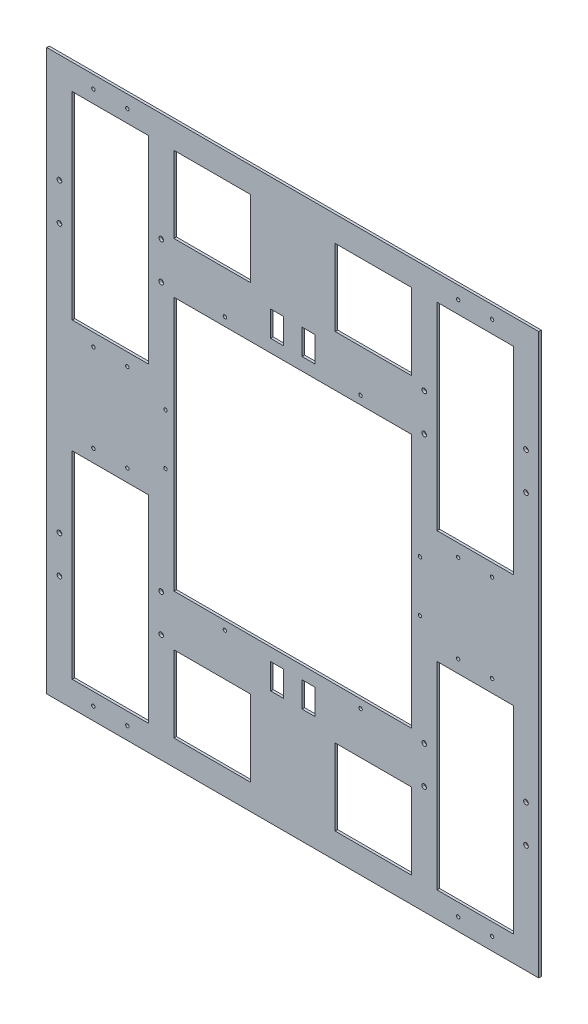
SolidWorks part; units mm, degrees
ref_plane "前基準面" through (0, 0, 0) normal (0, 0, 1) x (1, 0, 0)
ref_plane "上基準面" through (0, 0, 0) normal (0, 1, 0) x (1, 0, 0)
ref_plane "右基準面" through (0, 0, 0) normal (1, 0, 0) x (0, 0, -1)
sketch "草圖1" plane through (0, 0, 0) normal (0, 0, 1) x (1, 0, 0)
  line L1 (-404.7939, 163.224) -> (175.2061, 163.224)
  line L2 (-404.7939, 163.224) -> (-404.7939, -496.776)
  line L3 (-404.7939, -496.776) -> (175.2061, -496.776)
  line L4 (175.2061, 163.224) -> (175.2061, -496.776)
  dimension "D1" = 580
  dimension "D2" = 660
extrude "填料-伸長1" add sketch "草圖1" along normal blind 3
sketch "草圖2" plane through (0, 0, 3) normal (0, 0, 1) x (1, 0, 0)
  line L0 (-404.7939, 163.224) -> (-404.7939, -496.776) construction
  line L1 (-374.7939, -233.546) -> (-284.7939, -233.546)
  line L2 (-374.7939, -233.546) -> (-374.7939, -466.776)
  line L3 (-374.7939, -466.776) -> (-284.7939, -466.776)
  line L4 (-284.7939, -233.546) -> (-284.7939, -466.776)
  line L5 (-404.7939, -496.776) -> (175.2061, -496.776) construction
  line L6 (-114.7939, -496.776) -> (-114.7939, -197.0102)
  line L7 (-404.7939, -166.776) -> (-133.7701, -166.776)
  line L8 (145.2061, -466.776) -> (55.2061, -466.776)
  line L9 (145.2061, -233.546) -> (145.2061, -466.776)
  line L10 (55.2061, -233.546) -> (55.2061, -466.776)
  line L11 (145.2061, -233.546) -> (55.2061, -233.546)
  line L12 (145.2061, -100.006) -> (55.2061, -100.006)
  line L13 (55.2061, -100.006) -> (55.2061, 133.224)
  line L14 (145.2061, -100.006) -> (145.2061, 133.224)
  line L15 (145.2061, 133.224) -> (55.2061, 133.224)
  line L16 (-374.7939, 133.224) -> (-284.7939, 133.224)
  line L17 (-284.7939, -100.006) -> (-284.7939, 133.224)
  line L18 (-374.7939, -100.006) -> (-374.7939, 133.224)
  line L19 (-374.7939, -100.006) -> (-284.7939, -100.006)
  dimension "D1" = 233.23
  dimension "D2" = 90
  dimension "D3" = 30
  dimension "D4" = 30
extrude "除料-伸長1" cut sketch "草圖2" against normal blind 3 contours L13 L15 L14 L12 | L10 L8 L9 L11 | L4 L3 L2 L1 | L17 L16 L18 L19
sketch "草圖3" plane through (0, 0, 3) normal (0, 0, 1) x (1, 0, 0)
  line L0 (-404.7939, 163.224) -> (-404.7939, -496.776) construction
  line L1 (-254.7939, -376.776) -> (-164.7939, -376.776)
  line L2 (-254.7939, -376.776) -> (-254.7939, -466.776)
  line L3 (-254.7939, -466.776) -> (-164.7939, -466.776)
  line L4 (-164.7939, -376.776) -> (-164.7939, -466.776)
  line L5 (-404.7939, -496.776) -> (175.2061, -496.776) construction
  line L6 (-114.7939, -496.776) -> (-114.7939, -197.0102) construction
  line L7 (-114.7939, -197.0102) -> (-114.7939, -297.5966)
  line L8 (-133.7701, -166.776) -> (-254.7939, -166.776)
  line L9 (-404.7939, -166.776) -> (-133.7701, -166.776) construction
  line L10 (25.2061, -376.776) -> (25.2061, -466.776)
  line L11 (25.2061, -466.776) -> (-64.7939, -466.776)
  line L12 (-64.7939, -376.776) -> (-64.7939, -466.776)
  line L13 (25.2061, -376.776) -> (-64.7939, -376.776)
  line L14 (25.2061, 43.224) -> (-64.7939, 43.224)
  line L15 (-64.7939, 43.224) -> (-64.7939, 133.224)
  line L16 (25.2061, 133.224) -> (-64.7939, 133.224)
  line L17 (25.2061, 43.224) -> (25.2061, 133.224)
  line L18 (-164.7939, 43.224) -> (-164.7939, 133.224)
  line L19 (-254.7939, 133.224) -> (-164.7939, 133.224)
  line L20 (-254.7939, 43.224) -> (-254.7939, 133.224)
  line L21 (-254.7939, 43.224) -> (-164.7939, 43.224)
  point P30 (0, 0)
  point P31 (0, 0)
  point P32 (0, 0)
  point P33 (0, 0)
  point P34 (0, 0)
  dimension "D1" = 90
  dimension "D2" = 90
  dimension "D3" = 150
  dimension "D4" = 30
extrude "除料-伸長2" cut sketch "草圖3" against normal through all contours L1 L4 L3 L2 | L12 L11 L10 L13 | L15 L16 L17 L14 | L18 L19 L20 L21
sketch "草圖4" plane through (0, 0, 3) normal (0, 0, 1) x (1, 0, 0)
  line L0 (-404.7939, 163.224) -> (-404.7939, -496.776) construction
  line L1 (-254.7939, -16.776) -> (25.2061, -16.776)
  line L2 (-254.7939, -16.776) -> (-254.7939, -316.776)
  line L3 (-254.7939, -316.776) -> (25.2061, -316.776)
  line L4 (25.2061, -16.776) -> (25.2061, -316.776)
  line L5 (175.2061, 163.224) -> (-404.7939, 163.224) construction
  dimension "D1" = 300
  dimension "D2" = 280
  dimension "D3" = 150
  dimension "D4" = 180
extrude "除料-伸長3" cut sketch "草圖4" against normal blind 3
sketch "草圖5" plane through (0, 0, 3) normal (0, 0, 1) x (1, 0, 0)
  line L1 (-103.7939, -331.776) -> (-88.7939, -331.776)
  line L2 (-103.7939, -331.776) -> (-103.7939, -361.776)
  line L3 (-103.7939, -361.776) -> (-88.7939, -361.776)
  line L4 (-88.7939, -331.776) -> (-88.7939, -361.776)
  line L5 (55.2061, -233.546) -> (55.2061, -466.776) construction
  line L6 (-404.7939, -496.776) -> (175.2061, -496.776) construction
  line L7 (-114.7939, -266.9471) -> (-114.7939, -305.9958)
  line L8 (-114.7939, -496.776) -> (-114.7939, -197.0102) construction
  line L9 (-214.841, -166.776) -> (-181.5469, -166.776)
  line L10 (-404.7939, -166.776) -> (-133.7701, -166.776) construction
  line L11 (-140.7939, -331.776) -> (-140.7939, -361.776)
  line L12 (-125.7939, -361.776) -> (-140.7939, -361.776)
  line L13 (-125.7939, -331.776) -> (-125.7939, -361.776)
  line L14 (-125.7939, -331.776) -> (-140.7939, -331.776)
  line L15 (-125.7939, -1.776) -> (-140.7939, -1.776)
  line L16 (-125.7939, -1.776) -> (-125.7939, 28.224)
  line L17 (-125.7939, 28.224) -> (-140.7939, 28.224)
  line L18 (-140.7939, -1.776) -> (-140.7939, 28.224)
  line L19 (-88.7939, -1.776) -> (-88.7939, 28.224)
  line L20 (-103.7939, 28.224) -> (-88.7939, 28.224)
  line L21 (-103.7939, -1.776) -> (-103.7939, 28.224)
  line L22 (-103.7939, -1.776) -> (-88.7939, -1.776)
  dimension "D1" = 30
  dimension "D2" = 15
  dimension "D3" = 144
  dimension "D4" = 135
extrude "除料-伸長4" cut sketch "草圖5" against normal blind 3 contours L14 L11 L12 L13 | L1 L4 L3 L2 | L17 L18 L15 L16 | L20 L19 L22 L21
sketch "草圖6" plane through (0, 0, 3) normal (0, 0, 1) x (1, 0, 0)
  line L0 (-374.7939, -233.546) -> (-284.7939, -233.546) construction
  line L1 (-284.7939, -233.546) -> (-284.7939, -466.776) construction
  line L2 (-374.7939, -233.546) -> (-374.7939, -466.776) construction
  line L3 (-374.7939, -350.161) -> (-293.3571, -350.161)
  line L4 (-114.7939, -197.0102) -> (-114.7939, -286.0305)
  line L5 (-114.7939, -496.776) -> (-114.7939, -197.0102) construction
  line L6 (-234.4775, -166.776) -> (-164.5146, -166.776)
  line L7 (-404.7939, -166.776) -> (-133.7701, -166.776) construction
  circle A0 centre (-349.7939, -218.546) radius 2
  circle A1 centre (-309.7939, -218.546) radius 2
  circle A2 centre (-309.7939, -481.776) radius 2
  circle A3 centre (-349.7939, -481.776) radius 2
  circle A4 centre (-349.7939, -218.546) radius 2
  circle A5 centre (-309.7939, -218.546) radius 2
  circle A6 centre (-309.7939, -481.776) radius 2
  circle A7 centre (-349.7939, -481.776) radius 2
  circle A8 centre (-349.7939, -218.546) radius 2
  circle A9 centre (-309.7939, -218.546) radius 2
  circle A10 centre (-309.7939, -481.776) radius 2
  circle A11 centre (-349.7939, -481.776) radius 2
  circle A12 centre (-349.7939, -218.546) radius 2
  circle A13 centre (-309.7939, -218.546) radius 2
  circle A14 centre (-309.7939, -481.776) radius 2
  circle A15 centre (-349.7939, -481.776) radius 2
  circle A16 centre (80.2061, -481.776) radius 2
  circle A17 centre (120.2061, -481.776) radius 2
  circle A18 centre (80.2061, -218.546) radius 2
  circle A19 centre (120.2061, -218.546) radius 2
  circle A20 centre (-309.7939, 148.224) radius 2
  circle A21 centre (-349.7939, 148.224) radius 2
  circle A22 centre (-309.7939, -115.006) radius 2
  circle A23 centre (-349.7939, -115.006) radius 2
  circle A24 centre (80.2061, -115.006) radius 2
  circle A25 centre (120.2061, -115.006) radius 2
  circle A26 centre (120.2061, 148.224) radius 2
  circle A27 centre (80.2061, 148.224) radius 2
  point P45 (0, 0)
  point P62 (0, 0)
  point P63 (0, 0)
  point P64 (0, 0)
  point P65 (0, 0)
  point P66 (0, 0)
  point P67 (0, 0)
  point P68 (0, 0)
  point P69 (0, 0)
  point P70 (0, 0)
  point P71 (0, 0)
  point P72 (0, 0)
  point P73 (0, 0)
  point P74 (0, 0)
  dimension "D1" = 4
  dimension "D2" = 4
  dimension "D3" = 15
  dimension "D4" = 25
  dimension "D5" = 15
  dimension "D6" = 25
extrude "除料-伸長5" cut sketch "草圖6" against normal through all contours A21 | A20 | A26 | A27 | A25 | A24 | A19 | A18 | A22 | A23 | A0 | A1 | A2 | A3 | A16 | A17
sketch "草圖7" plane through (0, 0, 3) normal (0, 0, 1) x (1, 0, 0)
  line L0 (-404.7939, 163.224) -> (-404.7939, -496.776) construction
  line L1 (-404.7939, -496.776) -> (175.2061, -496.776) construction
  line L2 (-329.7939, -466.776) -> (-329.7939, -408.4096)
  line L3 (-374.7939, -466.776) -> (-284.7939, -466.776) construction
  line L4 (-114.7939, -285.3877) -> (-114.7939, -368.776)
  line L5 (-114.7939, -496.776) -> (-114.7939, -197.0102) construction
  line L6 (-169.3165, -166.776) -> (-252.8365, -166.776)
  line L7 (-404.7939, -166.776) -> (-133.7701, -166.776) construction
  line L8 (-114.7939, -48.1642) -> (-114.7939, 35.224)
  line L9 (-329.7939, 133.224) -> (-329.7939, 74.8577)
  circle A0 centre (-389.7939, -368.776) radius 2.75
  circle A1 centre (-389.7939, -324.776) radius 2.75
  circle A2 centre (-269.7939, -324.776) radius 2.75
  circle A3 centre (-269.7939, -368.776) radius 2.75
  circle A4 centre (-389.7939, -368.776) radius 2.75
  circle A5 centre (-389.7939, -324.776) radius 2.75
  circle A6 centre (-269.7939, -324.776) radius 2.75
  circle A7 centre (-269.7939, -368.776) radius 2.75
  circle A8 centre (40.2061, -368.776) radius 2.75
  circle A9 centre (40.2061, -324.776) radius 2.75
  circle A10 centre (160.2061, -324.776) radius 2.75
  circle A11 centre (160.2061, -368.776) radius 2.75
  circle A12 centre (40.2061, -368.776) radius 2.75
  circle A13 centre (40.2061, -324.776) radius 2.75
  circle A14 centre (160.2061, -324.776) radius 2.75
  circle A15 centre (160.2061, -368.776) radius 2.75
  circle A16 centre (160.2061, 35.224) radius 2.75
  circle A17 centre (160.2061, -8.776) radius 2.75
  circle A18 centre (40.2061, -8.776) radius 2.75
  circle A19 centre (40.2061, 35.224) radius 2.75
  circle A20 centre (160.2061, 35.224) radius 2.75
  circle A21 centre (160.2061, -8.776) radius 2.75
  circle A22 centre (40.2061, -8.776) radius 2.75
  circle A23 centre (40.2061, 35.224) radius 2.75
  circle A24 centre (-269.7939, 35.224) radius 2.75
  circle A25 centre (-269.7939, -8.776) radius 2.75
  circle A26 centre (-389.7939, -8.776) radius 2.75
  circle A27 centre (-389.7939, 35.224) radius 2.75
  circle A28 centre (-269.7939, 35.224) radius 2.75
  circle A29 centre (-269.7939, -8.776) radius 2.75
  circle A30 centre (-389.7939, -8.776) radius 2.75
  circle A31 centre (-389.7939, 35.224) radius 2.75
  point P68 (0, 0)
  point P69 (0, 0)
  point P70 (0, 0)
  point P71 (0, 0)
  point P72 (0, 0)
  point P73 (0, 0)
  dimension "D1" = 5.5
  dimension "D2" = 5.5
  dimension "D3" = 15
  dimension "D4" = 15
  dimension "D5" = 128
  dimension "D6" = 44
extrude "除料-伸長6" cut sketch "草圖7" against normal through all contours A27 | A26 | A25 | A24 | A18 | A19 | A17 | A16 | A11 | A10 | A9 | A8 | A2 | A3 | A0 | A1
sketch "草圖8" plane through (0, 0, 3) normal (0, 0, 1) x (1, 0, 0)
  line L0 (25.2061, -16.776) -> (-254.7939, -16.776) construction
  line L1 (-254.7939, -16.776) -> (-254.7939, -316.776) construction
  line L2 (25.2061, -316.776) -> (25.2061, -16.776) construction
  line L3 (-226.588, -166.776) -> (-181.3535, -166.776)
  line L4 (-404.7939, -166.776) -> (-133.7701, -166.776) construction
  line L6 (-114.7939, -197.0102) -> (-114.7939, -279.5926)
  line L7 (-114.7939, -496.776) -> (-114.7939, -197.0102) construction
  circle A0 centre (-194.7939, -6.776) radius 2
  circle A1 centre (-34.7939, -6.776) radius 2
  circle A2 centre (-34.7939, -326.776) radius 2
  circle A3 centre (-194.7939, -326.776) radius 2
  circle A4 centre (-264.7939, -136.776) radius 2
  circle A5 centre (-264.7939, -196.776) radius 2
  circle A6 centre (-264.7939, -136.776) radius 2
  circle A7 centre (-264.7939, -196.776) radius 2
  circle A8 centre (35.2061, -136.776) radius 2
  circle A9 centre (35.2061, -196.776) radius 2
  point P22 (0, 0)
  point P23 (0, 0)
  dimension "D1" = 4
  dimension "D2" = 4
  dimension "D3" = 10
  dimension "D4" = 60
  dimension "D5" = 60
  dimension "D6" = 4
  dimension "D7" = 4
  dimension "1" = 8
  dimension "D9" = 10
extrude "除料-伸長7" cut sketch "草圖8" against normal blind 3 contours A4 | A5 | A8 | A9 | A3 | A2 | A1 | A0
